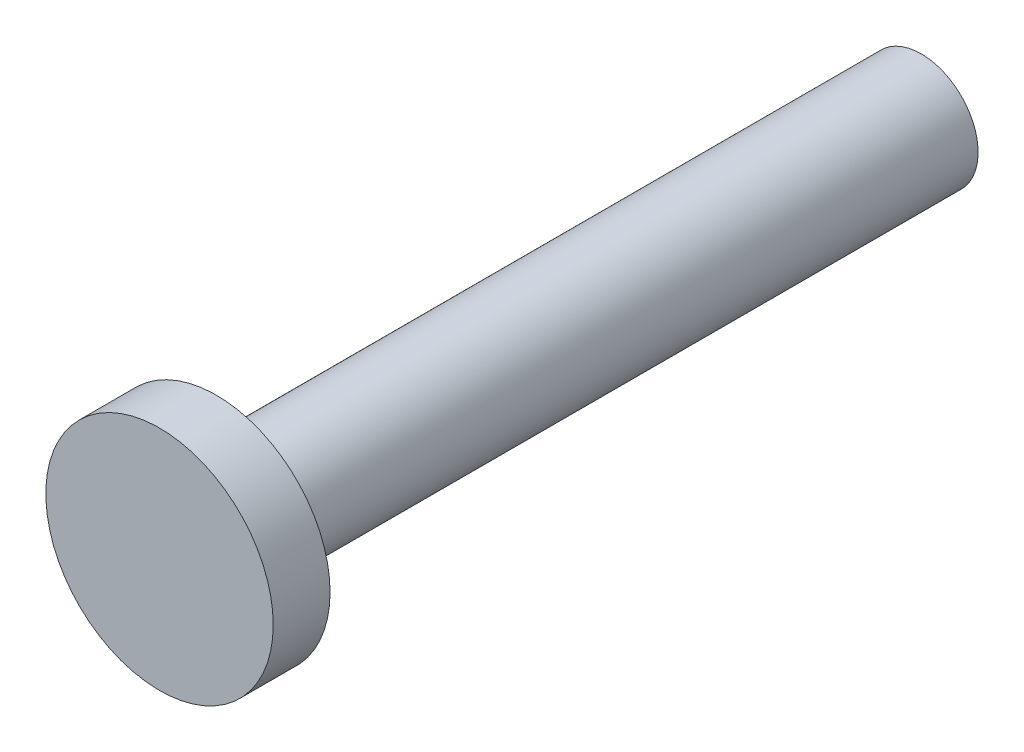
SolidWorks part; units mm, degrees
ref_plane "Front Plane" through (0, 0, 0) normal (0, 0, 1) x (1, 0, 0)
ref_plane "Top Plane" through (0, 0, 0) normal (0, 1, 0) x (1, 0, 0)
ref_plane "Right Plane" through (0, 0, 0) normal (1, 0, 0) x (0, 0, -1)
sketch "Sketch1" plane through (0, 0, 0) normal (0, 0, 1) x (1, 0, 0)
  circle A0 centre (0, 0) radius 2.54
  dimension "D1" = 5.08
extrude "Boss-Extrude1" add sketch "Sketch1" along normal blind 1.27
sketch "Sketch2" plane through (0, 0, 0) normal (0, 0, -1) x (-1, 0, 0)
  circle A0 centre (0, 0) radius 1.27
  dimension "D1" = 2.54
extrude "Boss-Extrude2" add sketch "Sketch2" along normal blind 15.748
